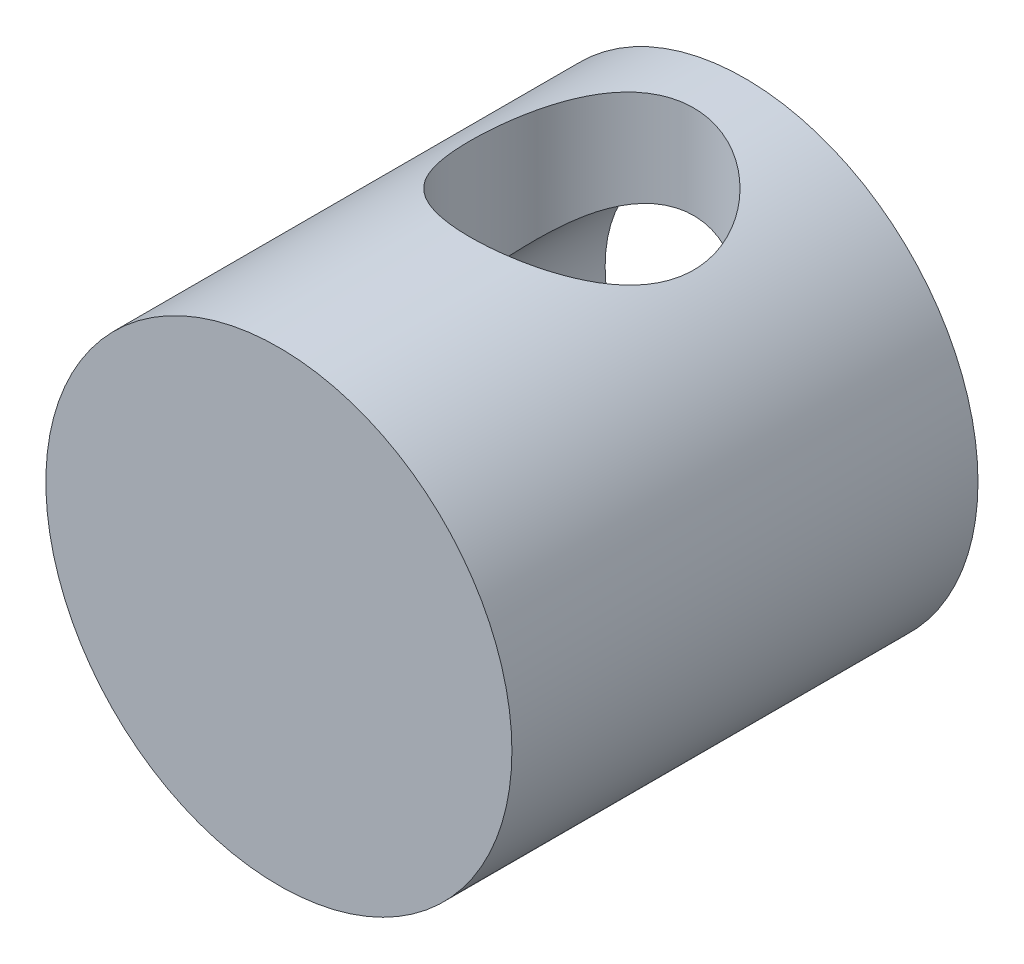
SolidWorks part; units mm, degrees
material "1.0036 (S235JRG1)"
ref_plane "Front Plane" through (0, 0, 0) normal (0, 0, 1) x (1, 0, 0)
ref_plane "Top Plane" through (0, 0, 0) normal (0, 1, 0) x (1, 0, 0)
ref_plane "Right Plane" through (0, 0, 0) normal (1, 0, 0) x (0, 0, -1)
sketch "Sketch1" plane through (0, 0, 0) normal (0, 0, 1) x (1, 0, 0)
  circle A0 centre (0, 0) radius 25
  dimension "D1" = 50
extrude "Boss-Extrude1" add sketch "Sketch1" along normal blind 50
sketch "Sketch2" plane through (0, 0, 0) normal (0, 0, -1) x (-1, 0, 0)
  circle A0 centre (0, 0) radius 15
extrude "Cut-Extrude1" cut sketch "Sketch2" against normal blind 30
ref_plane "Plane1" through (0, 25, 0) normal (0, 1, 0) x (1, 0, 0)
sketch "Sketch3" plane through (0, 25, 0) normal (0, 1, 0) x (1, 0, 0)
  line L0 (0, 0) -> (0, -17.5) construction
  circle A0 centre (0, -17.5) radius 12
extrude "Cut-Extrude2" cut sketch "Sketch3" against normal through all
